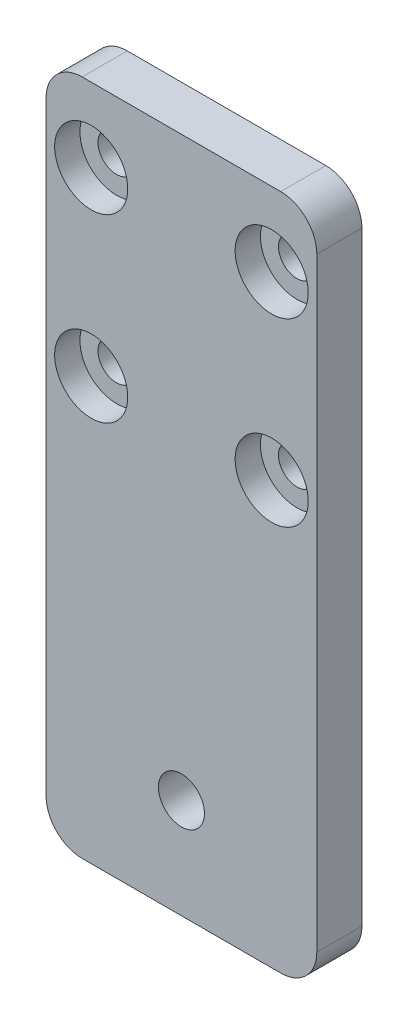
SolidWorks part; units mm, degrees
ref_plane "Alzado" through (0, 0, 0) normal (0, 0, 1) x (1, 0, 0)
ref_plane "Planta" through (0, 0, 0) normal (0, 1, 0) x (1, 0, 0)
ref_plane "Vista lateral" through (0, 0, 0) normal (1, 0, 0) x (0, 0, -1)
sketch "Croquis1" plane through (0, 0, 0) normal (0, 0, 1) x (1, 0, 0)
  line L0 (5, 46.8) -> (25, 66.8) construction
  line L1 (0, 75) -> (30, 75)
  line L2 (0, 75) -> (0, 0)
  line L3 (0, 0) -> (30, 0)
  line L4 (30, 75) -> (30, 0)
  line L5 (15, 56.8) -> (15, 75) construction
  circle A0 centre (5, 66.8) radius 2.05
  circle A1 centre (25, 66.8) radius 2.05
  circle A4 centre (25, 46.8) radius 2.05
  circle A5 centre (5, 46.8) radius 2.05
  circle A6 centre (15, 11.08) radius 2.55
  dimension "D3" = 4.1
  dimension "D11" = 5.1
  dimension "D1" = 30
  dimension "D2" = 75
  dimension "D4" = 20
  dimension "D5" = 63.92
  dimension "D6" = 8.2
  dimension "D7" = 20
extrude "Saliente-Extruir1" add sketch "Croquis1" along normal blind 5
fillet "Redondeo1" radius 4 4 edges at (0, 0, 2.5) (30, 0, 2.5) (0, 75, 2.5) (30, 75, 2.5)
sketch "Croquis4" plane through (0, 0, 5) normal (0, 0, 1) x (1, 0, 0)
  circle A0 centre (5, 66.8) radius 4.05
  circle A1 centre (5, 46.8) radius 4.05
  circle A2 centre (25, 46.8) radius 4.05
  circle A3 centre (25, 66.8) radius 4.05
  dimension "D1" = 8.1
extrude "Cortar-Extruir1" cut sketch "Croquis4" against normal blind 2.8
